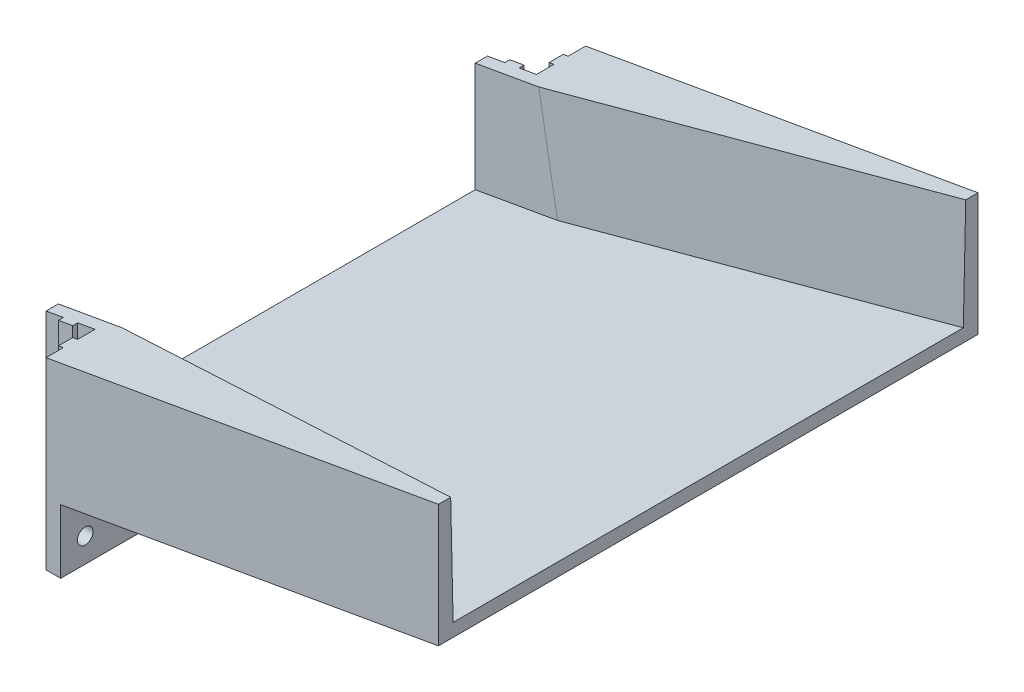
SolidWorks part; units mm, degrees
ref_plane "Front Plane" through (0, 0, 0) normal (0, 0, 1) x (1, 0, 0)
ref_plane "Top Plane" through (0, 0, 0) normal (0, 1, 0) x (1, 0, 0)
ref_plane "Right Plane" through (0, 0, 0) normal (1, 0, 0) x (0, 0, -1)
sketch "Esquisse1" plane through (0, 0, 0) normal (0, 0, 1) x (1, 0, 0)
  line L2 (0, 0) -> (13, 0)
  line L3 (13, 0) -> (13, 13)
  line L4 (13, 13) -> (90, 26.5772)
  line L5 (90, 26.5772) -> (90, 51.5772)
  line L6 (90, 51.5772) -> (0, 35.7077)
  line L7 (0, 35.7077) -> (0, 0)
  dimension "D1" = 13
  dimension "D2" = 100
  dimension "D3" = 25
  dimension "D4" = 90
  dimension "D5" = 13
extrude "Main" add sketch "Esquisse1" along normal mid plane 110
sketch "Esquisse3" plane through (-3.2945, 0, 0) normal (0, 1, 0) x (1, 0, 0)
  line L0 (3.2945, 45) -> (6.8445, 45)
  line L2 (6.8445, 45) -> (6.8445, 46)
  line L3 (6.8445, 46) -> (9.7445, 46)
  line L4 (9.7445, 46) -> (9.7445, 45)
  line L5 (9.7445, 45) -> (13.2945, 45)
  line L6 (13.2945, 45) -> (13.2945, 48.55)
  line L7 (13.2945, 48.55) -> (12.2945, 48.55)
  line L8 (12.2945, 48.55) -> (12.2945, 51.45)
  line L9 (12.2945, 51.45) -> (13.2945, 51.45)
  line L10 (13.2945, 51.45) -> (13.2945, 55)
  line L11 (93.2945, 55) -> (3.2945, 55) construction
  line L12 (13.2945, 55) -> (3.2945, 55)
  line L13 (3.2945, 55) -> (3.2945, 45)
  line L14 (3.2945, -55) -> (3.2945, 55) construction
  dimension "D1" = 2.9
  dimension "D2" = 10
  dimension "D3" = 10
  dimension "D4" = 1
extrude "Fixing" cut sketch "Esquisse3" along normal through all
sketch "Esquisse4" plane through (13, 0, 0) normal (1, 0, 0) x (0, 0, -1)
  line L1 (-55, 0) -> (-55, 13) construction
  line L2 (-55, 0) -> (55, 0) construction
  circle A1 centre (-50, 5) radius 1.6
  point P0 (-50.5988, 6.0258)
  dimension "D1" = 3.2
  dimension "D2" = 5
  dimension "D3" = 5
extrude "Enlèv. mat.-Extru.6" cut sketch "Esquisse4" against normal through all
mirror "Symétrie1" about plane through (0, 0, 0) normal (0, 0, 1) of "Enlèv. mat.-Extru.6", "Fixing"
sketch "Esquisse2" plane through (-6.1064, 34.631, 0) normal (-0.1736, 0.9848, 0) x (0.9848, 0.1736, 0)
  line L0 (97.589, 52.5) -> (97.589, -52.5)
  line L1 (97.589, -55) -> (97.589, 55) construction
  line L2 (-3.7994, -42.5) -> (19.3549, -42.5)
  line L3 (-3.7994, 42.5) -> (19.3549, 42.5)
  line L4 (-3.7994, -42.5) -> (-3.7994, 42.5)
  line L5 (19.3549, 42.5) -> (97.589, 52.5)
  line L6 (6.2006, -45) -> (6.2006, 45) construction
  line L7 (19.3549, -42.5) -> (97.589, -52.5)
  line L8 (16.3549, 51.45) -> (16.3549, 55) construction
  point P4 (97.589, 0)
  point P6 (18.0873, -42.5)
  point P10 (97.589, 0)
  point P12 (-3.7994, -41.4706)
  point P13 (6.2006, 0)
  point P23 (-3.7994, 0)
  dimension "D1" = 105
  dimension "D2" = 85
  dimension "D3" = 10
  dimension "D4" = 3
extrude "Central Hole" cut sketch "Esquisse2" against normal blind 22
